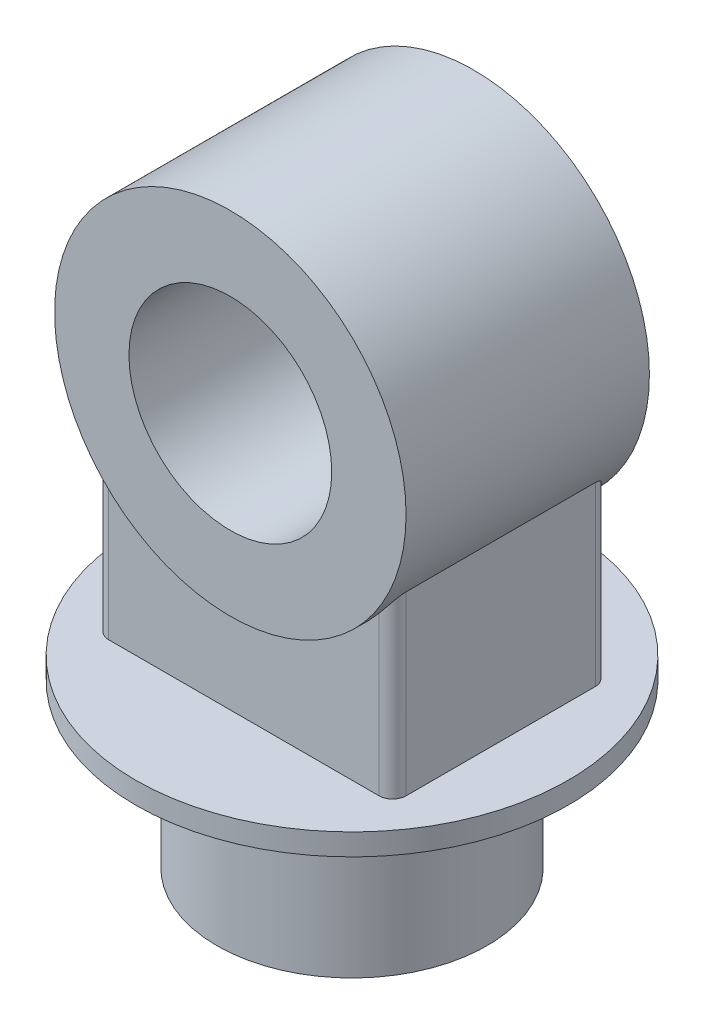
SolidWorks part; units mm, degrees
material "201 Annealed Stainless Steel (SS)"
ref_plane "Front Plane" through (0, 0, 0) normal (0, 0, 1) x (1, 0, 0)
ref_plane "Top Plane" through (0, 0, 0) normal (0, 1, 0) x (1, 0, 0)
ref_plane "Right Plane" through (0, 0, 0) normal (1, 0, 0) x (0, 0, -1)
sketch "Sketch1" plane through (0, 0, 0) normal (0, 1, 0) x (1, 0, 0)
  circle A0 centre (0, 0) radius 100
  dimension "D1" = 200
extrude "Boss-Extrude1" add sketch "Sketch1" along normal blind 120
sketch "Sketch2" plane through (0, 120, 0) normal (0, 1, 0) x (1, 0, 0)
  circle A0 centre (0, 0) radius 160
  dimension "D1" = 320
extrude "Boss-Extrude2" add sketch "Sketch2" along normal blind 16
sketch "Sketch3" plane through (0, 0, 0) normal (0, 0, 1) x (1, 0, 0)
  line L0 (160, 136) -> (-160, 136) construction
  circle A0 centre (0, 336) radius 75
  circle A1 centre (0, 336) radius 130
  dimension "D2" = 150
  dimension "D3" = 260
  dimension "D1" = 200
extrude "Boss-Extrude3" add sketch "Sketch3" along normal mid plane 180 separate body
sketch "Sketch4" plane through (0, 136, 0) normal (0, 1, 0) x (1, 0, 0)
  line L1 (-110, 80) -> (110, 80)
  line L2 (-110, 80) -> (-110, -80)
  line L3 (-110, -80) -> (110, -80)
  line L4 (110, 80) -> (110, -80)
  line L5 (0, -80) -> (0, 80) construction
  line L6 (-110, 0) -> (110, 0) construction
  point P0 (0, 0)
  dimension "D1" = 220
  dimension "D2" = 160
extrude "Boss-Extrude4" add sketch "Sketch4" along normal up to next
fillet "Fillet1" radius 10 4 edges at (-110, 201.359, 80) (-110, 201.359, -80) (110, 201.359, -80) (110, 201.359, 80)
